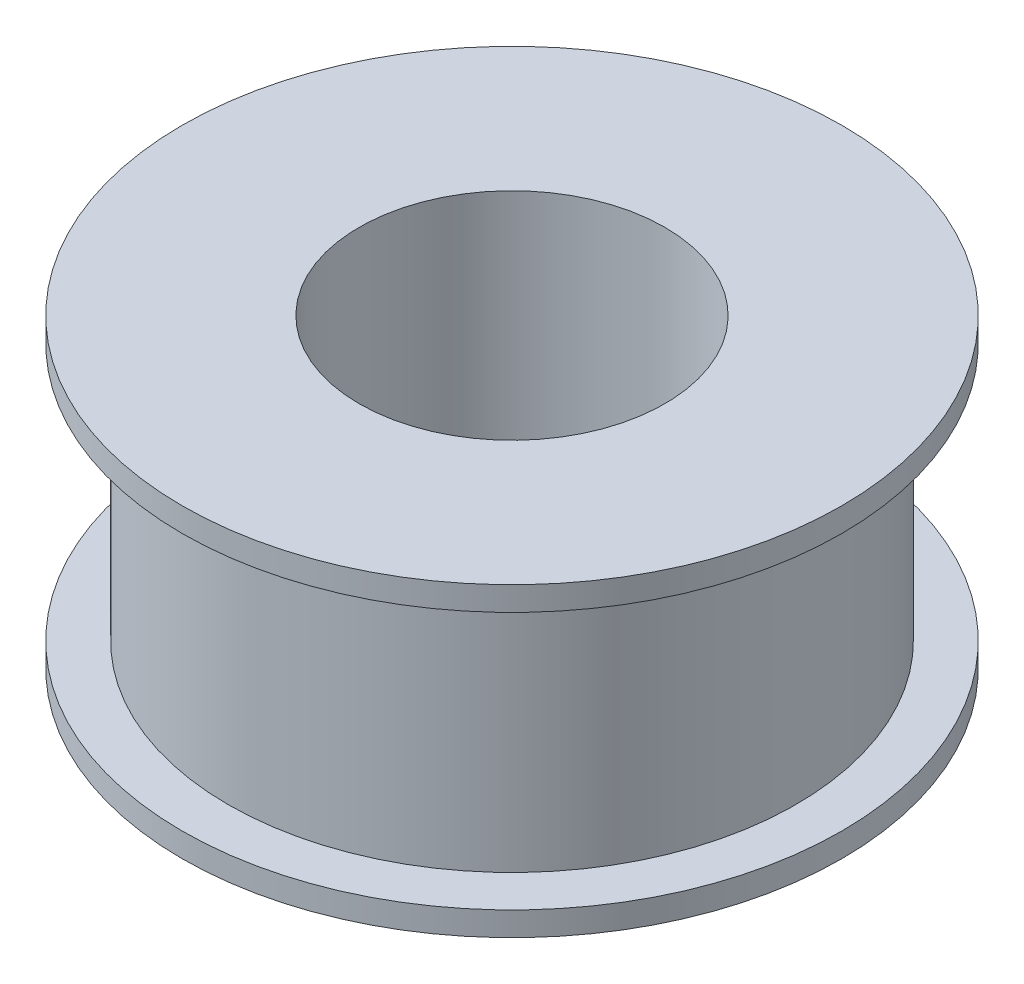
SolidWorks part; units mm, degrees
ref_plane "Front Plane" through (0, 0, 0) normal (0, 0, 1) x (1, 0, 0)
ref_plane "Top Plane" through (0, 0, 0) normal (0, 1, 0) x (1, 0, 0)
ref_plane "Right Plane" through (0, 0, 0) normal (1, 0, 0) x (0, 0, -1)
sketch "Sketch1" plane through (0, 0, 0) normal (1, 0, 0) x (0, 0, -1)
  line L0 (-18.4323, 0) -> (10.6512, 0) construction
  line L1 (-7, -7) -> (-7, 7)
  line L2 (-7, 7) -> (-15.1, 7)
  line L3 (-15.1, 7) -> (-15.1, 5.9)
  line L4 (-15.1, 5.9) -> (-13, 5.9)
  line L5 (-13, 5.9) -> (-13, -5.9)
  line L7 (-15.1, -5.9) -> (-13, -5.9)
  line L8 (-15.1, -7) -> (-15.1, -5.9)
  line L9 (-7, -7) -> (-15.1, -7)
  point P10 (-13, 0)
  point P13 (-7, 0)
  dimension "D1" = 8.1
  dimension "D2" = 7
  dimension "D3" = 7
  dimension "D4" = 13
  dimension "D5" = 1.1
ref_axis "Axis1" through (0, 7.7, 0) along (0, -1, 0)
revolve "Revolve1" add sketch "Sketch1" angle 360 about axis through (0, 7.7, 0) along (0, -1, 0)
